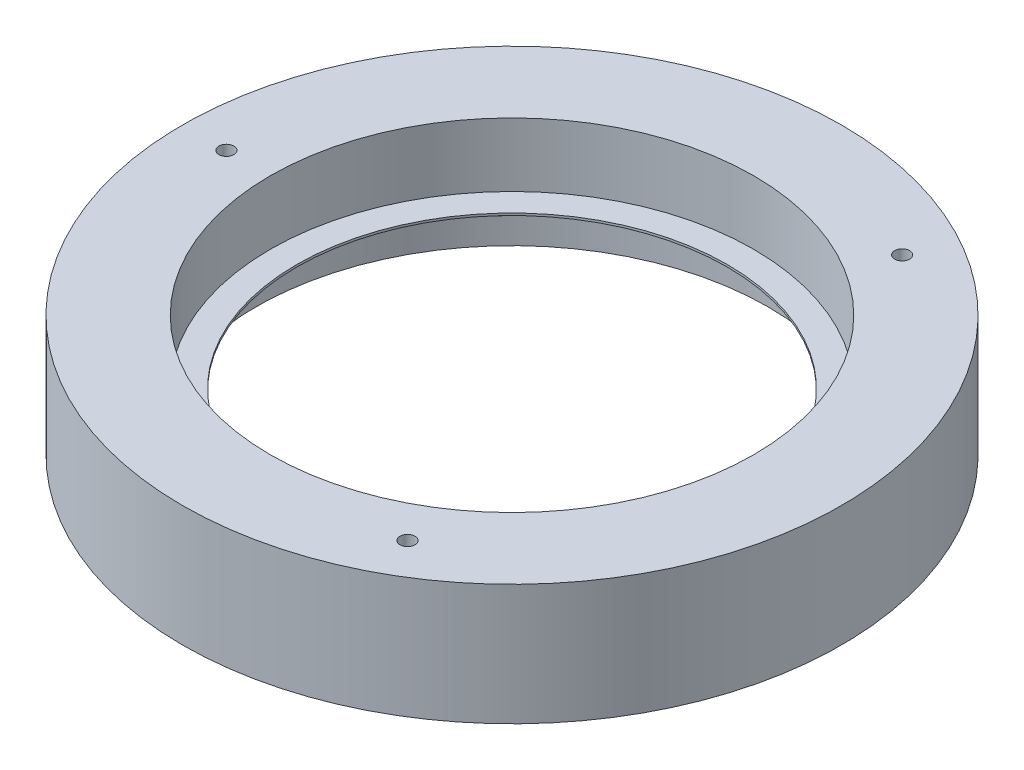
SolidWorks part; units mm, degrees
material "PLA"
ref_plane "Alzado" through (0, 0, 0) normal (0, 0, 1) x (1, 0, 0)
ref_plane "Planta" through (0, 0, 0) normal (0, 1, 0) x (1, 0, 0)
ref_plane "Vista lateral" through (0, 0, 0) normal (1, 0, 0) x (0, 0, -1)
sketch "Croquis1" plane through (0, 0, 0) normal (0, 0, 1) x (1, 0, 0)
  line L0 (58.283, 6) -> (58.283, 0)
  line L1 (58.283, 0) -> (75, 0)
  line L2 (75, 0) -> (75, 27.5)
  line L3 (75, 27.5) -> (55, 27.5)
  line L4 (55, 27.5) -> (55, 13)
  line L5 (55, 13) -> (49, 13)
  line L7 (49, 13) -> (49, 12.5)
  line L8 (49, 12.5) -> (58.283, 6)
  line L9 (0, 0) -> (0, 57.6728) construction
  dimension "D1" = 55
  dimension "D2" = 6
  dimension "D3" = 75
  dimension "D4" = 27.5
  dimension "D5" = 0.5
  dimension "D6" = 13
  dimension "D7" = 6
  dimension "D8" = 145
revolve "Revolución1" add sketch "Croquis1" angle 360 about L9
sketch "Croquis2" plane through (0, 27.5, 0) normal (0, 1, 0) x (1, 0, 0)
  circle A0 centre (-65, 0) radius 1.7
  dimension "D1" = 3.4
  dimension "D2" = 65
extrude "Cortar-Extruir1" cut sketch "Croquis2" against normal blind 59
pattern_circular "MatrizC1" count 3 over 360 about axis through (0, 0, 0) along (0, 1, 0) of "Cortar-Extruir1"
